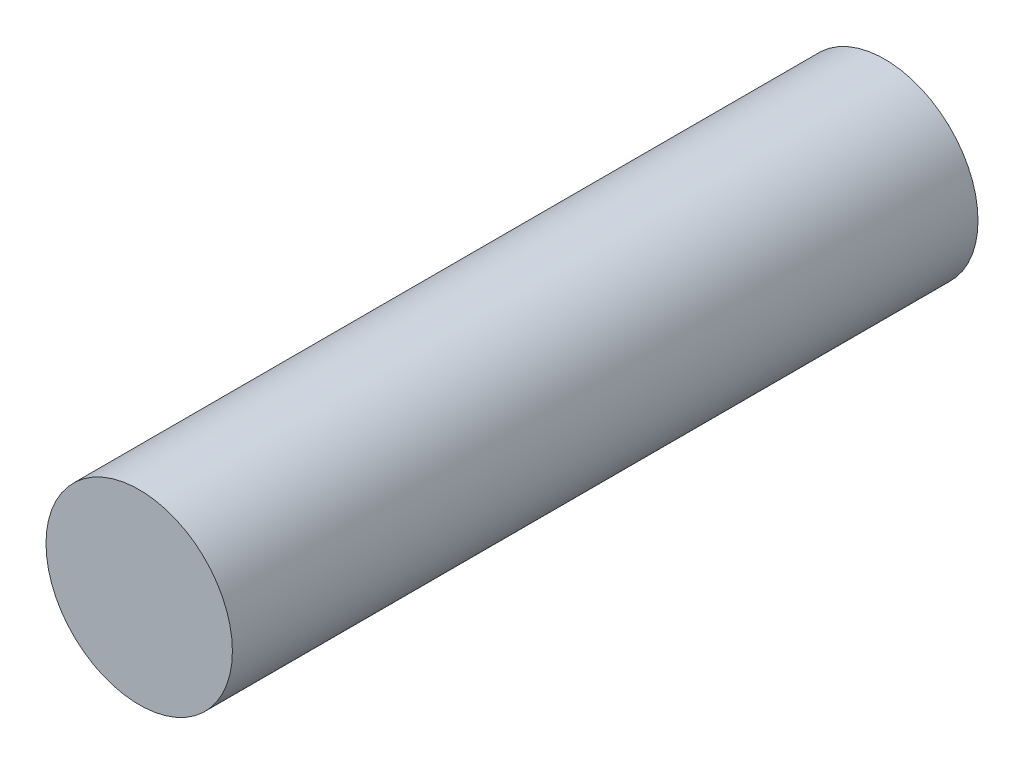
SolidWorks part; units mm, degrees
ref_plane "Front Plane" through (0, 0, 0) normal (0, 0, 1) x (1, 0, 0)
ref_plane "Top Plane" through (0, 0, 0) normal (0, 1, 0) x (1, 0, 0)
ref_plane "Right Plane" through (0, 0, 0) normal (1, 0, 0) x (0, 0, -1)
sketch "Sketch1" plane through (0, 0, 0) normal (0, 0, 1) x (1, 0, 0)
  circle A0 centre (0, 0) radius 1.5
  dimension "D1" = 3
extrude "Boss-Extrude1" add sketch "Sketch1" along normal blind 12
